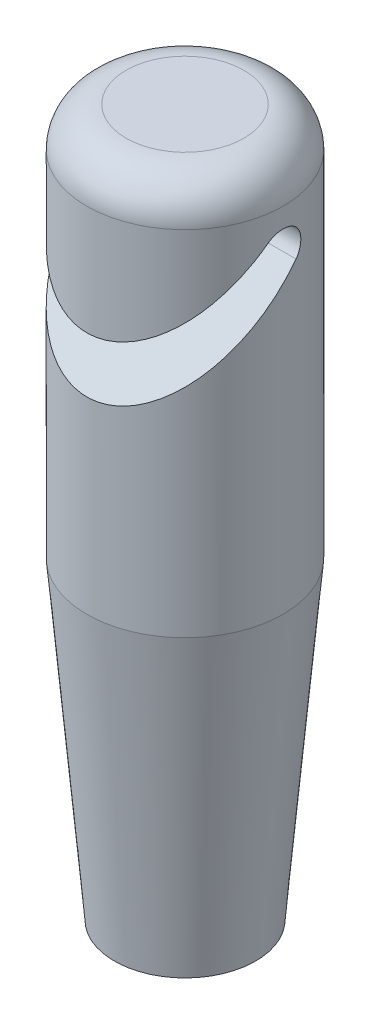
SolidWorks part; units mm, degrees
ref_plane "Front Plane" through (0, 0, 0) normal (0, 0, 1) x (1, 0, 0)
ref_plane "Top Plane" through (0, 0, 0) normal (0, 1, 0) x (1, 0, 0)
ref_plane "Right Plane" through (0, 0, 0) normal (1, 0, 0) x (0, 0, -1)
sketch "Sketch1" plane through (0, 0, 0) normal (0, 1, 0) x (1, 0, 0)
  circle A1 centre (0, 0) radius 2.5
  dimension "D2" = 5
extrude "Boss-Extrude1" add sketch "Sketch1" along normal blind 10
sketch "Sketch2" plane through (0, 0, 0) normal (0, -1, 0) x (1, 0, 0)
  circle A1 centre (0, 0) radius 2.5
  circle A2 centre (0, 0) radius 2.5
  dimension "D1" = 0
extrude "Boss-Extrude2" add sketch "Sketch2" along normal blind 8 draft 5
sketch "Sketch3" plane through (0, -8, 0) normal (0, -1, 0) x (1, 0, 0)
  circle A0 centre (0, 0) radius 1.5
  dimension "D1" = 3
extrude "Cut-Extrude1" cut sketch "Sketch3" against normal up to surface (8 mm away)
fillet "Fillet1" radius 1 1 edges at (0, 10, 2.5)
sketch "Sketch4" plane through (0, 0, 0) normal (1, 0, 0) x (0, 0, -1)
  line L0 (0, 8) -> (-2.5, 5.5) construction
  line L1 (-2.5, 9) -> (-2.5, 0) construction
  line L2 (0, 8) -> (0.3536, 7.6464) construction
  line L3 (0.3536, 7.6464) -> (-6.4183, 0.8746)
  line L4 (-6.4183, 0.8746) -> (-6.4183, 2.2888)
  line L5 (-6.4183, 2.2888) -> (-0.3536, 8.3536)
  line L6 (0, 8) -> (-0.3536, 8.3536) construction
  arc A0 (0.3536, 7.6464) -> (-0.3536, 8.3536) centre (0, 8) ccw
  dimension "D1" = 1
  dimension "D2" = 45
  dimension "D3" = 8
extrude "Cut-Extrude2" cut sketch "Sketch4" against normal through all both and the other way through all
